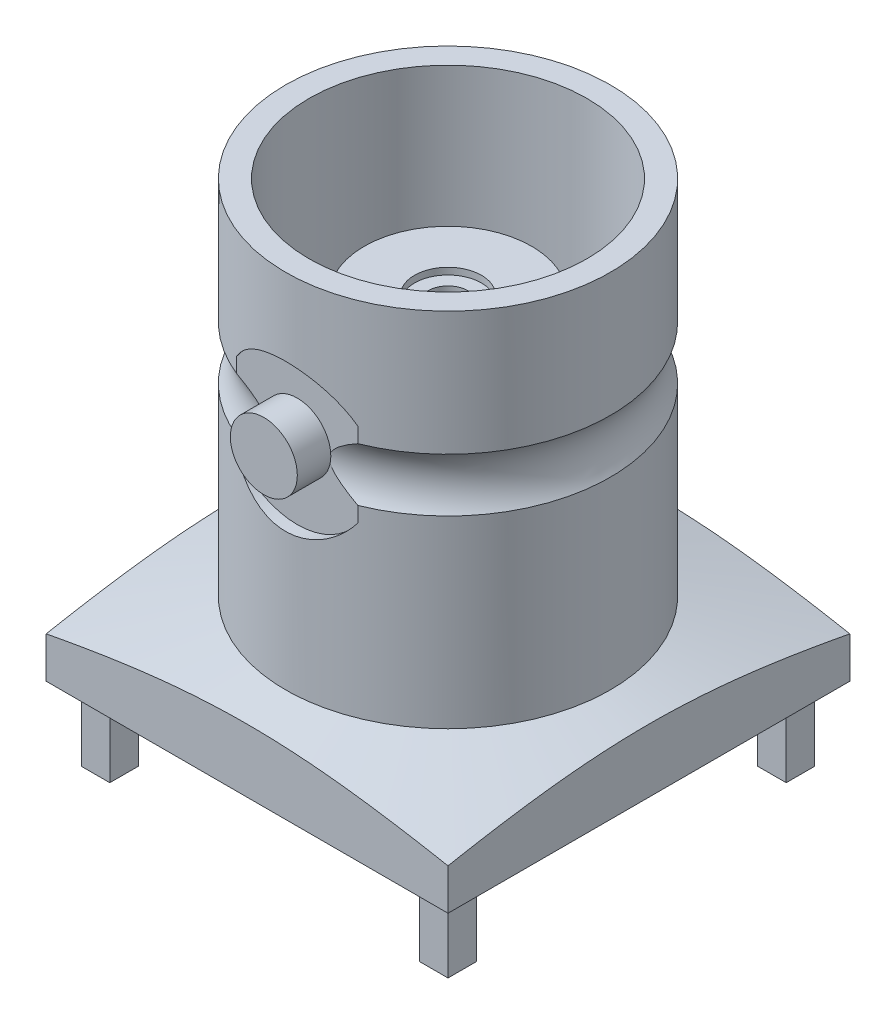
SolidWorks part; units mm, degrees
ref_plane "Plan de face" through (0, 0, 0) normal (0, 0, 1) x (1, 0, 0)
ref_plane "Plan de dessus" through (0, 0, 0) normal (0, 1, 0) x (1, 0, 0)
ref_plane "Plan de droite" through (0, 0, 0) normal (1, 0, 0) x (0, 0, -1)
sketch "Esquisse1" plane through (0, 0, 0) normal (0, 0, 1) x (1, 0, 0)
  line L0 (0, 0) -> (-10, 0)
  line L1 (-10, 0) -> (-10, 0.8201)
  line L2 (-10, 0.8201) -> (-4.85, 2.2)
  line L4 (-4.85, 13) -> (-4.15, 13)
  line L5 (-4.15, 13) -> (-4.15, 5)
  line L6 (-4.15, 5) -> (-2.5, 5)
  line L7 (-2.5, 5) -> (-2.5, 10)
  line L8 (-2.5, 10) -> (-1, 10)
  line L9 (-1, 10) -> (-1, 9.8)
  line L10 (-1, 9.8) -> (0, 9.8)
  line L11 (0, 9.8) -> (0, 0)
  line L12 (-4.85, 13) -> (-4.85, 9.2984)
  line L13 (-4.85, 7.7016) -> (-4.85, 2.2)
  arc A1 (-4.85, 9.2984) -> (-4.85, 7.7016) centre (-6, 8.5) cw
  point P3 (-4.85, 7.6379)
  point P16 (0, 0)
  point P17 (0, 0)
  dimension "D3" = 1.4
  dimension "D1" = 2.2
  dimension "D2" = 10.8
  dimension "D4" = 10
  dimension "D5" = 15
  dimension "D6" = 4.15
  dimension "D7" = 2.5
  dimension "D8" = 1
  dimension "D9" = 3
  dimension "D10" = 0.2
  dimension "D11" = 8
  dimension "D12" = 4.5
  dimension "D13" = 4.85
  dimension "D14" = 6
revolve "Révolution1" add sketch "Esquisse1" angle 360 about L11
sketch "Esquisse2" plane through (0, 0, 0) normal (0, 1, 0) x (1, 0, 0)
  line L1 (-6, -6) -> (6, -6)
  line L2 (-6, -6) -> (-6, 6)
  line L3 (-6, 6) -> (6, 6)
  line L4 (6, -6) -> (6, 6)
  line L5 (-6, -6) -> (6, 6) construction
  line L6 (-6, 6) -> (6, -6) construction
  line L7 (-11, -11) -> (11, -11)
  line L8 (-11, -11) -> (-11, 11)
  line L9 (-11, 11) -> (11, 11)
  line L10 (11, -11) -> (11, 11)
  line L11 (-11, -11) -> (11, 11) construction
  line L12 (-11, 11) -> (11, -11) construction
  point P0 (0, 0)
  point P6 (0, 0)
  dimension "D1" = 22
  dimension "D2" = 22
  dimension "D3" = 12
  dimension "D4" = 12
extrude "Enlèv. mat.-Extru.4" cut sketch "Esquisse2" against normal through all and the other way through all
sketch "Esquisse3" plane through (0, 0, 0) normal (0, -1, 0) x (1, 0, 0)
  line L1 (5.05, 5.05) -> (-5.05, 5.05) construction
  line L2 (5.05, 5.05) -> (5.05, -5.05) construction
  line L3 (5.05, -5.05) -> (-5.05, -5.05) construction
  line L4 (-5.05, 5.05) -> (-5.05, -5.05) construction
  line L5 (5.05, 5.05) -> (-5.05, -5.05) construction
  line L6 (5.05, -5.05) -> (-5.05, 5.05) construction
  line L7 (5.475, -5.475) -> (4.625, -5.475)
  line L8 (5.475, -5.475) -> (5.475, -4.625)
  line L9 (5.475, -4.625) -> (4.625, -4.625)
  line L10 (4.625, -5.475) -> (4.625, -4.625)
  line L11 (5.475, -5.475) -> (4.625, -4.625) construction
  line L12 (5.475, -4.625) -> (4.625, -5.475) construction
  line L13 (-4.625, -5.475) -> (-5.475, -5.475)
  line L14 (-4.625, -5.475) -> (-4.625, -4.625)
  line L15 (-4.625, -4.625) -> (-5.475, -4.625)
  line L16 (-5.475, -5.475) -> (-5.475, -4.625)
  line L17 (-4.625, -5.475) -> (-5.475, -4.625) construction
  line L18 (-4.625, -4.625) -> (-5.475, -5.475) construction
  line L19 (-4.625, 5.475) -> (-5.475, 5.475)
  line L20 (-4.625, 5.475) -> (-4.625, 4.625)
  line L21 (-4.625, 4.625) -> (-5.475, 4.625)
  line L22 (-5.475, 5.475) -> (-5.475, 4.625)
  line L23 (-4.625, 5.475) -> (-5.475, 4.625) construction
  line L24 (-4.625, 4.625) -> (-5.475, 5.475) construction
  line L25 (5.475, 5.475) -> (4.625, 5.475)
  line L26 (5.475, 5.475) -> (5.475, 4.625)
  line L27 (5.475, 4.625) -> (4.625, 4.625)
  line L28 (4.625, 5.475) -> (4.625, 4.625)
  line L29 (5.475, 5.475) -> (4.625, 4.625) construction
  line L30 (5.475, 4.625) -> (4.625, 5.475) construction
  point P0 (0, 0)
  dimension "D1" = 10.1
  dimension "D2" = 10.1
  dimension "D3" = 0.85
extrude "Boss.-Extru.1" add sketch "Esquisse3" along normal blind 2.2
sketch "Esquisse4" plane through (0, 9.8, 0) normal (0, 1, 0) x (1, 0, 0)
  circle A0 centre (0, 0) radius 0.6
  dimension "D1" = 1.2
extrude "Enlèv. mat.-Extru.5" cut sketch "Esquisse4" against normal blind 2
sketch "Esquisse5" plane through (0, 0, 6) normal (0, 0, 1) x (1, 0, 0)
  line L0 (0, 13) -> (0, 8.5) construction
  line L1 (4.15, 13) -> (-4.15, 13) construction
  circle A0 centre (0, 8.5) radius 2.2
  dimension "D1" = 4.4
  dimension "D2" = 4.5
extrude "Enlèv. mat.-Extru.6" cut sketch "Esquisse5" against normal blind 1.5
sketch "Esquisse6" plane through (0, 0, 4.5) normal (0, 0, 1) x (1, 0, 0)
  circle A0 centre (0, 8.5742) radius 1
  dimension "D1" = 2
extrude "Boss.-Extru.2" add sketch "Esquisse6" along normal blind 1
mirror "Symétrie1" about plane through (0, 0, 0) normal (0, 0, 1) of "Boss.-Extru.2", "Enlèv. mat.-Extru.6"
sketch "Esquisse7" plane through (0, 0, 0) normal (0, -1, 0) x (1, 0, 0)
  circle A0 centre (0, 0) radius 0.5
  dimension "D1" = 1
extrude "Boss.-Extru.3" add sketch "Esquisse7" along normal blind 2.4
chamfer "Chanfrein1" distance 0.2 angle 45 1 edges at (0.5, -2.4, 0)
